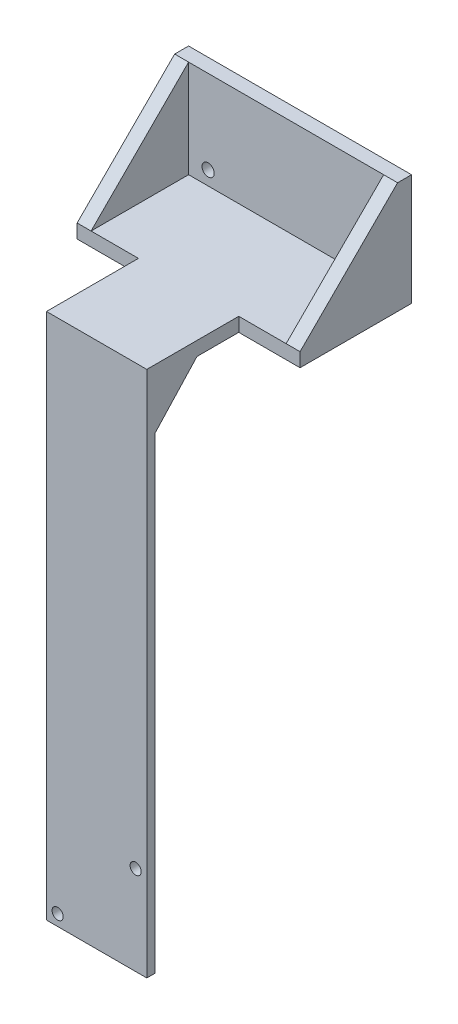
SolidWorks part; units mm, degrees
ref_plane "Front Plane" through (0, 0, 0) normal (0, 0, 1) x (1, 0, 0)
ref_plane "Top Plane" through (0, 0, 0) normal (0, 1, 0) x (1, 0, 0)
ref_plane "Right Plane" through (0, 0, 0) normal (1, 0, 0) x (0, 0, -1)
sketch "Sketch1" plane through (0, 0, 0) normal (0, 1, 0) x (1, 0, 0)
  line L1 (-40, -20) -> (40, -20)
  line L2 (-40, -20) -> (-40, 20)
  line L3 (-40, 20) -> (40, 20)
  line L4 (40, -20) -> (40, 20)
  line L5 (-40, -20) -> (40, 20) construction
  line L6 (-40, 20) -> (40, -20) construction
  point P0 (0, 0)
  dimension "D1" = 80
  dimension "D2" = 40
extrude "Boss-Extrude1" add sketch "Sketch1" along normal blind 5
sketch "Sketch2" plane through (0, 5, 0) normal (0, 1, 0) x (1, 0, 0)
  line L0 (-40, 20) -> (-40, -20) construction
  line L1 (40, 20) -> (-40, 20)
  line L2 (40, 20) -> (40, 15)
  line L3 (40, 15) -> (-40, 15)
  line L4 (-40, 20) -> (-40, 15)
  dimension "D1" = 5
extrude "Boss-Extrude2" add sketch "Sketch2" along normal blind 35
sketch "Sketch3" plane through (-40, 0, 0) normal (-1, 0, 0) x (0, 0, 1)
  line L0 (-15, 40) -> (20, 5)
  line L1 (20, 5) -> (-15, 5)
  line L2 (-15, 40) -> (-15, 5)
extrude "Boss-Extrude3" add sketch "Sketch3" against normal blind 5
sketch "Sketch4" plane through (40, 0, 0) normal (1, 0, 0) x (0, 0, -1)
  line L0 (15, 40) -> (-20, 5)
  line L1 (-20, 5) -> (15, 5)
  line L2 (15, 5) -> (15, 40)
extrude "Boss-Extrude4" add sketch "Sketch4" against normal blind 5
sketch "Sketch6" plane through (0, 0, -15) normal (0, 0, 1) x (1, 0, 0)
  line L0 (-40, 0) -> (40, 0) construction
  line L1 (-40, 5) -> (-40, 40) construction
  line L2 (0, 0) -> (0, 18.0603) construction
  circle A0 centre (-28, 10) radius 2.2
  circle A1 centre (28, 10) radius 2.2
  dimension "D1" = 4.4
  dimension "D2" = 10
  dimension "D3" = 12
extrude "Cut-Extrude2" cut sketch "Sketch6" against normal through all
sketch "Sketch7" plane through (0, 0, 20) normal (0, 0, 1) x (1, 0, 0)
  line L0 (-40, 0) -> (40, 0) construction
  line L1 (-18, 5) -> (18, 5)
  line L2 (-18, 5) -> (-18, 0)
  line L3 (-18, 0) -> (18, 0)
  line L4 (18, 5) -> (18, 0)
  line L5 (40, 5) -> (40, 0) construction
  line L6 (-40, 5) -> (-40, 0) construction
  dimension "D1" = 22
  dimension "D2" = 22
  dimension "D3" = 5
extrude "Boss-Extrude5" add sketch "Sketch7" along normal blind 33
sketch "Sketch8" plane through (0, 0, 0) normal (0, -1, 0) x (1, 0, 0)
  line L0 (18, 53) -> (18, 20) construction
  line L1 (-18, 53) -> (18, 53)
  line L2 (-18, 53) -> (-18, 50)
  line L3 (-18, 50) -> (18, 50)
  line L4 (18, 53) -> (18, 50)
  dimension "D1" = 3
extrude "Boss-Extrude6" add sketch "Sketch8" along normal blind 184.15
sketch "Sketch9" plane through (-18, 0, 0) normal (-1, 0, 0) x (0, 0, 1)
  line L0 (35, 0) -> (50, -16.2455)
  line L1 (50, 0) -> (20, 0) construction
  line L2 (50, -184.15) -> (50, 0) construction
  line L3 (50, -16.2455) -> (50, 0)
  line L4 (50, 0) -> (35, 0)
extrude "Boss-Extrude7" add sketch "Sketch9" against normal blind 36
sketch "Sketch10" plane through (0, 0, 53) normal (0, 0, 1) x (1, 0, 0)
  line L0 (18, -184.15) -> (-18, -184.15) construction
  line L1 (18, -148.15) -> (-18, -148.15) construction
  line L2 (18, -184.15) -> (18, 5) construction
  line L3 (-18, 5) -> (-18, -184.15) construction
  line L4 (-18, -148.15) -> (18, -184.15) construction
  circle A0 centre (14, -152.15) radius 2
  circle A1 centre (-14, -180.15) radius 2
  dimension "D2" = 4
  dimension "D1" = 36
  dimension "D3" = 4
  dimension "D4" = 4
extrude "Cut-Extrude3" cut sketch "Sketch10" against normal blind 3
